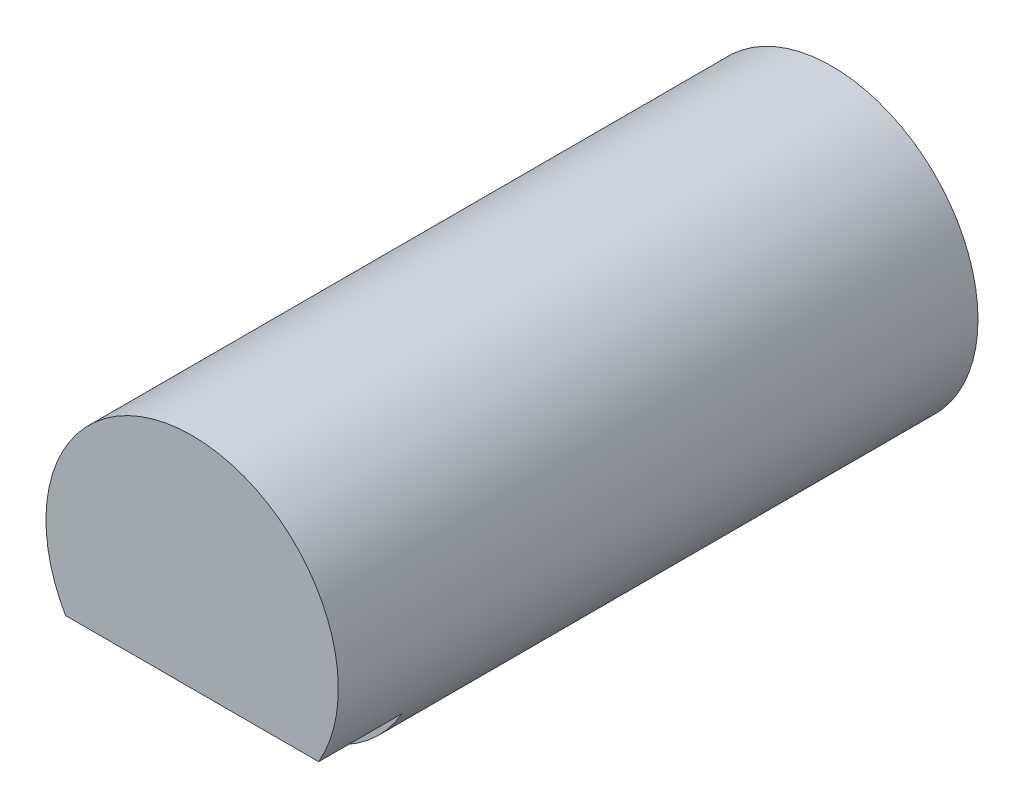
SolidWorks part; units mm, degrees
ref_plane "Front Plane" through (0, 0, 0) normal (0, 0, 1) x (1, 0, 0)
ref_plane "Top Plane" through (0, 0, 0) normal (0, 1, 0) x (1, 0, 0)
ref_plane "Right Plane" through (0, 0, 0) normal (1, 0, 0) x (0, 0, -1)
sketch "Sketch1" plane through (0, 0, 0) normal (0, 0, 1) x (1, 0, 0)
  circle A0 centre (-166.3618, 44.9023) radius 5.9267 construction
  circle A1 centre (-166.3618, 44.9023) radius 5.9267
extrude "Boss-Extrude1" add sketch "Sketch1" along normal blind 22.552
sketch "Sketch2" plane through (0, 0, 22.552) normal (0, 0, 1) x (1, 0, 0)
  line L0 (-166.3618, 44.9023) -> (-166.3618, 38.9757)
  line L1 (-166.3618, 41.939) -> (-161.2292, 41.939)
  line L2 (-166.3618, 41.939) -> (-171.4945, 41.939)
  circle A1 centre (-166.3618, 44.9023) radius 5.9267
  circle A2 centre (-166.3618, 44.9023) radius 5.9267
  dimension "D1" = 0
extrude "Boss-Extrude2" add sketch "Sketch2" along normal blind 3.3867
